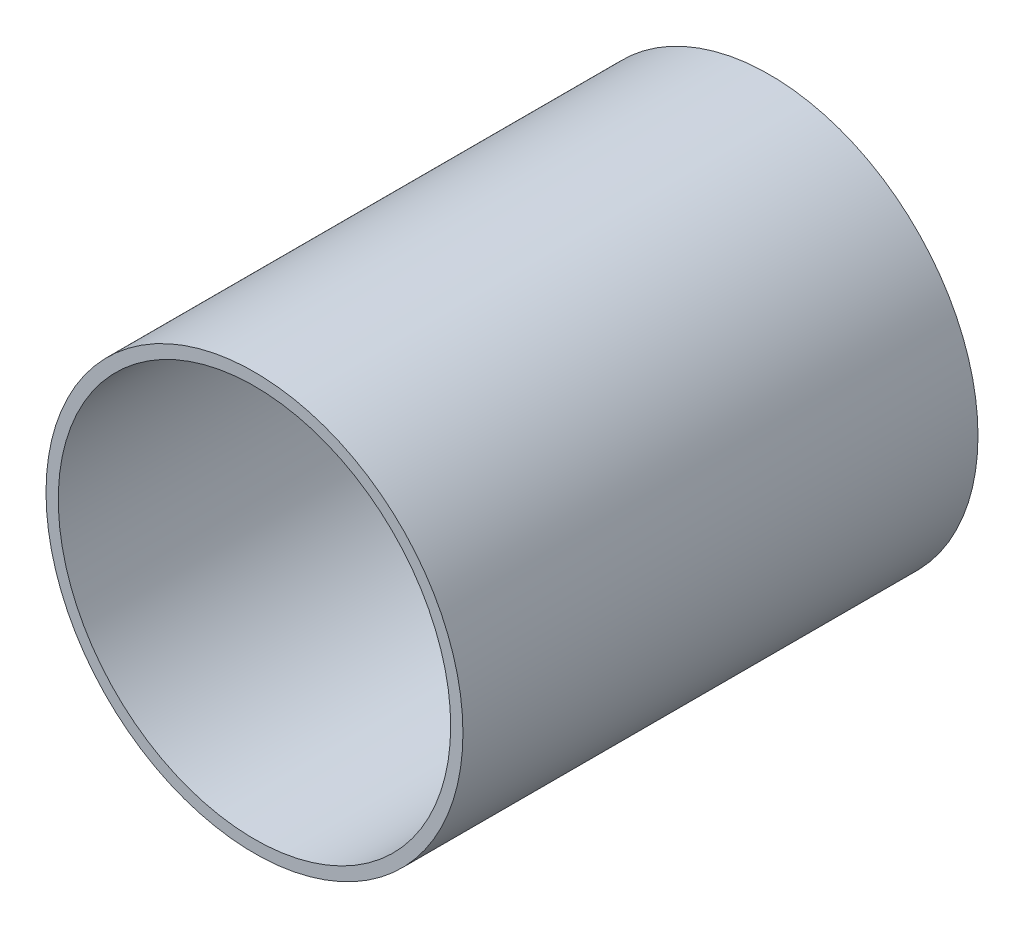
SolidWorks part; units mm, degrees
ref_plane "Front Plane" through (0, 0, 0) normal (0, 0, 1) x (1, 0, 0)
ref_plane "Top Plane" through (0, 0, 0) normal (0, 1, 0) x (1, 0, 0)
ref_plane "Right Plane" through (0, 0, 0) normal (1, 0, 0) x (0, 0, -1)
sketch "Sketch1" plane through (0, 0, 0) normal (0, 0, 1) x (1, 0, 0)
  circle A0 centre (0, 0) radius 53.975
extrude "Boss-Extrude1" add sketch "Sketch1" along normal blind 6.35
sketch "Sketch2" plane through (0, 0, 6.35) normal (0, 0, 1) x (1, 0, 0)
  line L0 (0, 53.975) -> (0, -53.975) construction
  line L1 (-53.975, 0) -> (53.975, 0) construction
  circle A0 centre (0, 0) radius 53.975 construction
  point P9 (0, 0)
hole_wizard "CSK for 1/4 Flat Head Machine Screw (100)1" positions "Sketch2" profile "Sketch3" countersink size "1/4" standard "ANSI Inch" end condition through all
sketch "Sketch3" plane through (0, 0, 6.35) normal (1, 0, 0) x (0, -1, 0)
  line L0 (0, 0) -> (0, 6.35)
  line L1 (0, 6.35) -> (3.3782, 6.35)
  line L2 (3.3782, 6.35) -> (3.3782, 2.5682)
  line L3 (3.3782, 2.5682) -> (6.4389, 0)
  line L5 (6.4389, 0) -> (0, 0)
  line L6 (-3.3782, 2.5682) -> (-6.4389, 0) construction
  line L11 (0, -6.35) -> (0, 107.95) construction
  dimension "Thru Hole Dia." = 6.7564
  dimension "Thru Hole Depth" = 6.35
  dimension "Near C'Sink Dia." = 12.8778
  dimension "Near C'Sink Angle" = 100
sketch "Sketch4" plane through (0, 0, 6.35) normal (0, 0, 1) x (1, 0, 0)
  circle A0 centre (0, 0) radius 53.975
  circle A1 centre (0, 0) radius 50.8
  dimension "D1" = 3.175
extrude "Boss-Extrude2" add sketch "Sketch4" along normal blind 127
